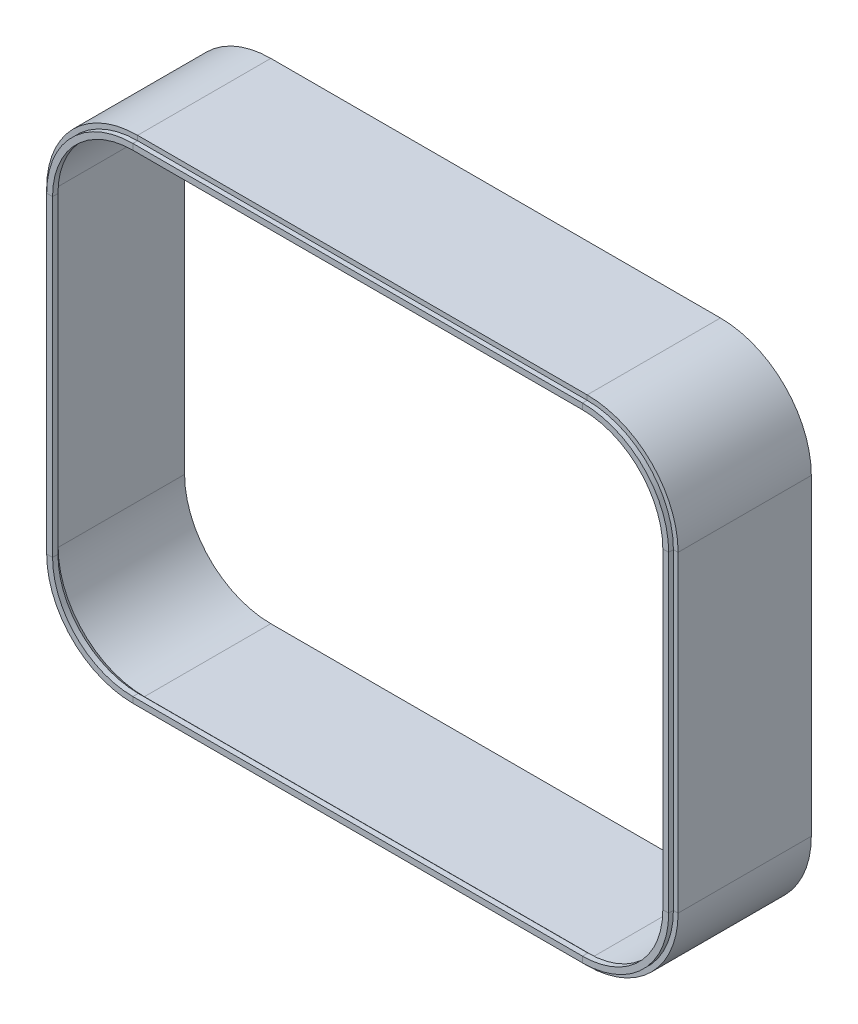
SolidWorks part; units mm, degrees
ref_plane "Front Plane" through (0, 0, 0) normal (0, 0, 1) x (1, 0, 0)
ref_plane "Top Plane" through (0, 0, 0) normal (0, 1, 0) x (1, 0, 0)
ref_plane "Right Plane" through (0, 0, 0) normal (1, 0, 0) x (0, 0, -1)
sketch "BasketRing" plane through (0, 0, 0) normal (0, 0, 1) x (1, 0, 0)
  line L1 (44, 0) -> (273.5, 0)
  line L2 (0, 44) -> (0, 203.5)
  line L3 (44, 247.5) -> (273.5, 247.5)
  line L4 (317.5, 44) -> (317.5, 203.5)
  line L5 (0, 0) -> (317.5, 247.5) construction
  line L6 (0, 247.5) -> (317.5, 0) construction
  arc A0 (273.5, 0) -> (317.5, 44) centre (273.5, 44) ccw
  arc A1 (317.5, 203.5) -> (273.5, 247.5) centre (273.5, 203.5) ccw
  arc A2 (0, 203.5) -> (44, 247.5) centre (44, 203.5) cw
  arc A3 (44, 0) -> (0, 44) centre (44, 44) cw
  point P4 (158.75, 123.75)
  dimension "D3" = 44
  dimension "D1" = 317.5
  dimension "D2" = 247.5
ref_plane "Plane1" through (44, 0, 0) normal (1, 0, 0) x (0, 0, -1)
ref_plane "Plane3" through (158.75, 0, 0) normal (1, 0, 0) x (0, 0, -1)
sketch "ShapeOf Edge" plane through (44, 0, 0) normal (1, 0, 0) x (0, 0, -1)
  line L32 (0, 0) -> (2.4, 0)
  line L33 (2.4, 0) -> (2.4, -2.4)
  line L34 (0, 0) -> (0, 3)
  line L35 (0, 44) -> (0, 0) construction
  line L36 (0, 3) -> (2.7483, 3)
  line L38 (5.8549, 0) -> (70.4, 0)
  line L39 (70.4, 0) -> (70.4, -2.4)
  line L40 (70.4, -2.4) -> (2.4, -2.4)
  line L44 (2.7483, 3) -> (5.8549, 0)
  point P2 (2.4, -2.4)
  point P3 (2.7661, 3)
  point P6 (2.7163, 3)
  dimension "D1" = 3
  dimension "D6" = 2.4
  dimension "D10" = 2.4
  dimension "D4" = 68
  dimension "D5" = 136
  dimension "D2" = 2.4
sweep "Sweep2" add profiles "ShapeOf Edge" path "BasketRing"
equation "\"height\"=68"
equation "\"D4@ShapeOf Edge\"=\"height\""
